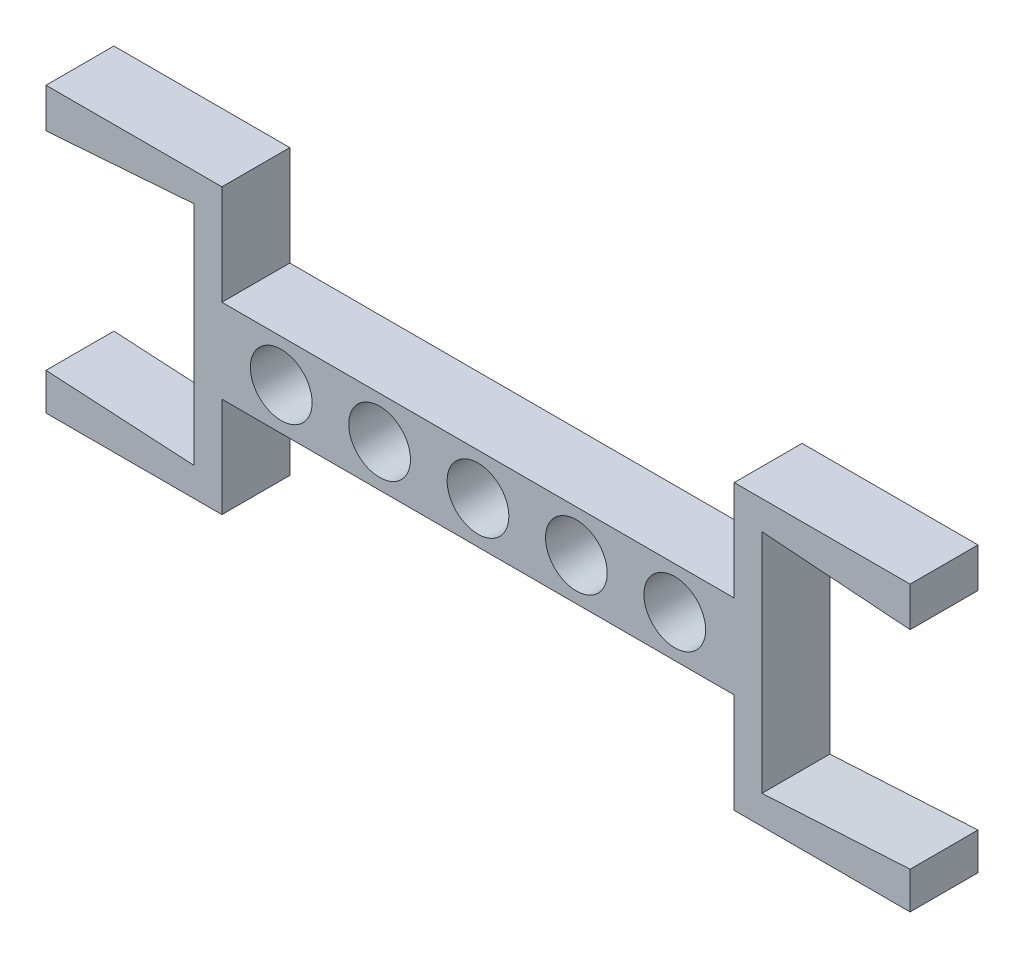
SolidWorks part; units mm, degrees
ref_plane "前基準面" through (0, 0, 0) normal (0, 0, 1) x (1, 0, 0)
ref_plane "上基準面" through (0, 0, 0) normal (0, 1, 0) x (1, 0, 0)
ref_plane "右基準面" through (0, 0, 0) normal (1, 0, 0) x (0, 0, -1)
sketch "草圖1" plane through (0, 0, 0) normal (0, 0, 1) x (1, 0, 0)
  line L5 (-50.2191, -29.5507) -> (-50.2191, -41.0782) construction
  line L10 (-1089.7522, -45.1921) -> (-85.2191, -45.1921) construction
  line L11 (-85.2191, -35.1921) -> (-70.9691, -35.1921)
  line L12 (-85.2191, -35.1921) -> (-85.2191, -55.1921)
  line L14 (-70.9691, -35.1921) -> (-70.9691, -41.7921)
  line L15 (-29.4691, -35.1921) -> (-29.4691, -41.7921)
  line L17 (-15.2191, -35.1921) -> (-15.2191, -55.1921)
  line L18 (-66.1641, -41.7921) -> (-29.4691, -41.7921)
  line L19 (-66.1641, -41.7921) -> (-70.9691, -41.7921)
  line L20 (-66.1641, -48.5921) -> (-29.4691, -48.5921)
  line L21 (-66.1641, -48.5921) -> (-70.9691, -48.5921)
  line L22 (-70.9691, -48.5921) -> (-70.9691, -55.1921)
  line L23 (-29.4691, -48.5921) -> (-29.4691, -55.1921)
  line L26 (-85.2191, -35.6333) -> (-85.2191, -54.7508)
  line L28 (-73.2163, -36.0144) -> (-73.2163, -54.3697)
  line L29 (-73.2163, -45.1921) -> (934.463, -45.1921) construction
  line L31 (-15.2191, -35.6333) -> (-15.2191, -54.7508)
  line L33 (-27.2219, -36.0144) -> (-27.2219, -54.3697)
  line L34 (-85.2191, -36.8921) -> (-73.2163, -36.0144)
  line L35 (-15.2191, -36.8921) -> (-27.2219, -36.0144)
  line L36 (-85.2191, -53.6921) -> (-73.2163, -54.3697)
  line L37 (-15.2191, -53.6921) -> (-27.2219, -54.3697)
  line L38 (-15.2191, -53.6921) -> (-15.2191, -55.1921)
  line L39 (-15.2191, -56.6921) -> (-29.4691, -56.6921)
  line L40 (-85.2191, -35.1921) -> (-70.9691, -35.1921)
  line L41 (-85.2191, -35.1921) -> (-85.2191, -33.6921)
  line L42 (-85.2191, -33.6921) -> (-70.9691, -33.6921)
  line L43 (-70.9691, -35.1921) -> (-70.9691, -33.6921)
  line L45 (-85.2191, -55.1921) -> (-85.2191, -56.6921)
  line L46 (-85.2191, -56.6921) -> (-70.9691, -56.6921)
  line L47 (-70.9691, -55.1921) -> (-70.9691, -56.6921)
  line L48 (-29.4691, -55.1921) -> (-29.4691, -56.6921)
  line L50 (-15.2191, -55.1921) -> (-15.2191, -56.6921)
  line L51 (-15.2191, -33.6921) -> (-29.4691, -33.6921)
  line L52 (-29.4691, -35.1921) -> (-29.4691, -33.6921)
  line L54 (-15.2191, -35.1921) -> (-15.2191, -33.6921)
  circle A0 centre (-66.1641, -45.1921) radius 2.5
  circle A1 centre (-58.1941, -45.1921) radius 2.5
  circle A2 centre (-50.2241, -45.1921) radius 2.5
  circle A3 centre (-42.2541, -45.1921) radius 2.5
  circle A4 centre (-34.2841, -45.1921) radius 2.5
  point P11 (-66.1641, -45.1921)
  point P15 (-34.2741, -45.1921)
  dimension "D3" = 20
  dimension "D1" = 15.945
  dimension "D4" = 1.0588
  dimension "D5" = 70
  dimension "D7" = 6.8
  dimension "D8" = 41.5
  dimension "D9" = 1.5
  dimension "D10" = 1.7
  dimension "D2" = 5
extrude "填料-伸長2" add sketch "草圖1" along normal blind 5.5
